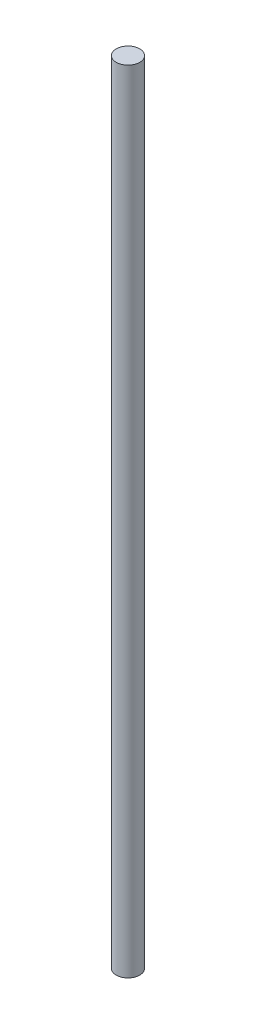
SolidWorks part; units mm, degrees
ref_plane "Front Plane" through (0, 0, 0) normal (0, 0, 1) x (1, 0, 0)
ref_plane "Top Plane" through (0, 0, 0) normal (0, 1, 0) x (1, 0, 0)
ref_plane "Right Plane" through (0, 0, 0) normal (1, 0, 0) x (0, 0, -1)
sketch "Sketch1" plane through (0, 0, 0) normal (0, 1, 0) x (1, 0, 0)
  circle A0 centre (0, 0) radius 5.5562
  dimension "D1" = 11.1125
extrude "Boss-Extrude1" add sketch "Sketch1" along normal blind 375
equation "\"m3 hole\"= 3.2"
equation "\"m4 hole\"= 4.2"
equation "\"m5 hole\"= 5.2"
equation "\"m6 hole\"= 6.2"
equation "\"m8 hole\"= 8.2"
equation "\"m3 tapped\"= 2.5"
equation "\"m4 tapped\"= 3.3"
equation "\"m5 tapped\"= 4.2"
equation "\"m6 tapped\"= 5"
equation "\"m8 tapped\"= 6.8"
